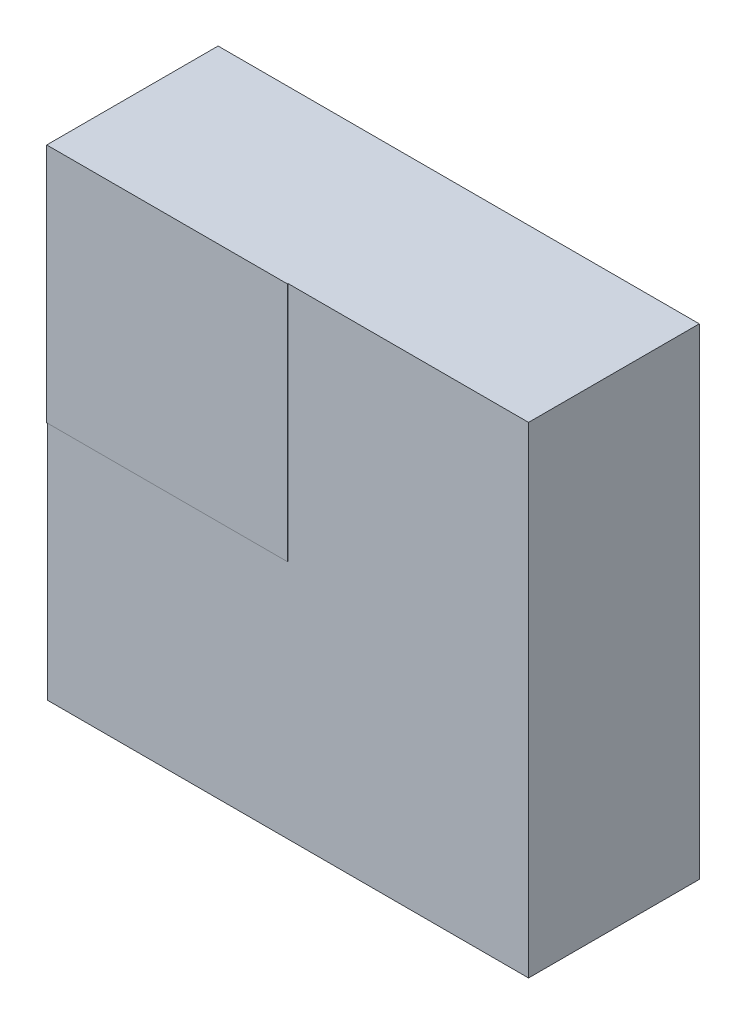
SolidWorks part; units mm, degrees
ref_plane "Front Plane" through (0, 0, 0) normal (0, 0, 1) x (1, 0, 0)
ref_plane "Top Plane" through (0, 0, 0) normal (0, 1, 0) x (1, 0, 0)
ref_plane "Right Plane" through (0, 0, 0) normal (1, 0, 0) x (0, 0, -1)
ref_plane "Plane2" through (0, 0, 0.13) normal (0, 0, 1) x (1, 0, 0)
sketch "Sketch1" plane through (0, 0, 0.13) normal (0, 0, 1) x (1, 0, 0)
  line L1 (-0.3805, -0.3805) -> (0.3805, -0.3805)
  line L2 (-0.3805, -0.3805) -> (-0.3805, 0.3805)
  line L3 (-0.3805, 0.3805) -> (0.3805, 0.3805)
  line L4 (0.3805, -0.3805) -> (0.3805, 0.3805)
  line L5 (-0.3805, -0.3805) -> (0.3805, 0.3805) construction
  line L6 (-0.3805, 0.3805) -> (0.3805, -0.3805) construction
  point P0 (0, 0)
  dimension "D1" = 0.761
  dimension "D2" = 0.761
extrude "Boss-Extrude1" add sketch "Sketch1" along normal blind 0.27
sketch "Sketch2" plane through (0, 0, 0.4) normal (0, 0, 1) x (1, 0, 0)
  line L1 (-0.3805, 0.3805) -> (0, 0.3805)
  line L2 (-0.3805, 0.3805) -> (-0.3805, 0)
  line L3 (-0.3805, 0) -> (0, 0)
  line L4 (0, 0.3805) -> (0, 0)
extrude "Boss-Extrude2" add sketch "Sketch2" along normal blind 0.001
ref_plane "Plane1" through (0, 0.2, 0) normal (0, 1, 0) x (1, 0, 0)
sketch "Sketch3" plane through (0, 0.2, 0) normal (0, 1, 0) x (1, 0, 0)
  line L0 (0.2, -0.13) -> (0.2, 0)
  line L2 (0.2, -0.13) -> (0.2954, -0.13)
  line L5 (0.3805, -0.13) -> (-0.3805, -0.13) construction
  arc A0 (0.2954, -0.13) -> (0.2, 0) centre (0.2, -0.1) ccw
  point P6 (0.2905, 0)
  dimension "D2" = 0.2
  dimension "D1" = 0.13
  dimension "D3" = 0.2
revolve "Revolve1" add sketch "Sketch3" angle 360 about L0
pattern_linear "LPattern1" count 2 spacing 0.4 along (-1, 0, 0) count 2 spacing 0.4 along (0, -1, 0) of "Revolve1"
